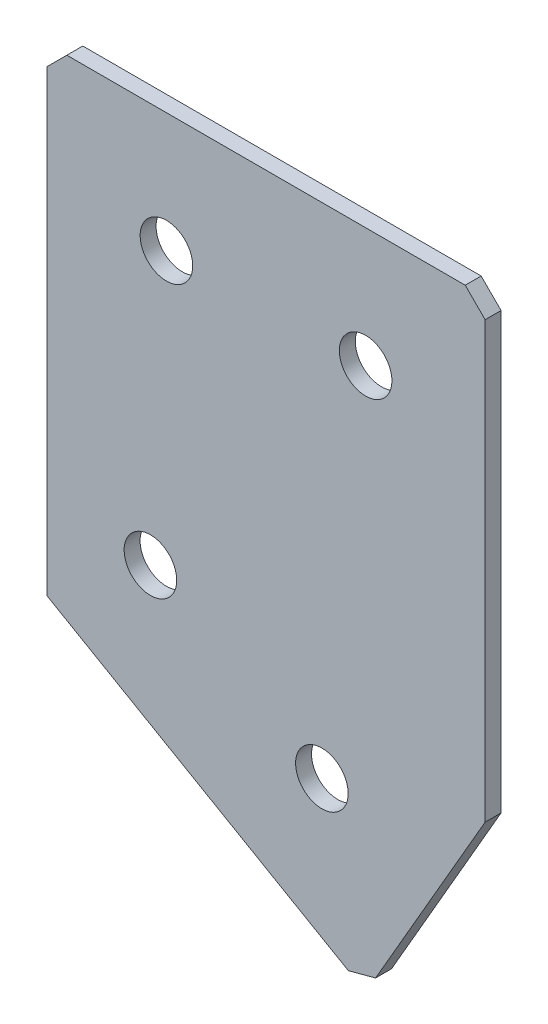
SolidWorks part; units mm, degrees
material "Простая углеродистая сталь"
ref_plane "Спереди" through (0, 0, 0) normal (0, 0, 1) x (1, 0, 0)
ref_plane "Сверху" through (0, 0, 0) normal (0, 1, 0) x (1, 0, 0)
ref_plane "Справа" through (0, 0, 0) normal (1, 0, 0) x (0, 0, -1)
sketch "Эскиз3" plane through (0, 0, 0) normal (0, 0, -1) x (1, 0, 0)
  line L0 (0, 0) -> (55, 0)
  line L1 (55, 0) -> (55, 57.1132)
  line L2 (0, 0) -> (0, 60)
  line L3 (0, 60) -> (40, 83.094)
  line L4 (40, 83.094) -> (55, 57.1132)
  dimension "D1" = 55
  dimension "D2" = 60
  dimension "D3" = 30
  dimension "D4" = 30
  dimension "D5" = 57.1132
extrude "Бобышка-Вытянуть1" add sketch "Эскиз3" along normal blind 2
hole_wizard "Отверстие с зазором M61" positions "Эскиз4" profile "Эскиз5" hole size "M6" standard "DIN" end condition through all
sketch "Эскиз4" plane through (0, 0, -2) normal (0, 0, -1) x (1, 0, 0)
  line L0 (12.9904, 50.1795) -> (34.5096, 62.6036) construction
  line L2 (40, 83.094) -> (0, 60) construction
  line L3 (15, 15) -> (40, 15) construction
  line L5 (0, 0) -> (55, 0) construction
  line L6 (0, 60) -> (0, 0) construction
  line L7 (55, 0) -> (55, 57.1132) construction
  line L8 (55, 57.1132) -> (40, 83.094) construction
  line L9 (12.9904, 50.1795) -> (0, 42.6795) construction
  point P0 (15, 15)
  point P2 (40, 15)
  point P4 (12.9904, 50.1795)
  point P6 (34.5096, 62.6036)
  dimension "D1" = 15
  dimension "D2" = 15
  dimension "D3" = 15
  dimension "D4" = 15
  dimension "D5" = 15
  dimension "D6" = 15
  dimension "D7" = 24.8483
  dimension "D8" = 25
sketch "Эскиз5" plane through (15, -15, -2) normal (1, 0, 0) x (0, 1, 0)
  line L0 (0, 0) -> (0, 2)
  line L1 (0, 2) -> (3.3, 2)
  line L2 (3.3, 2) -> (3.3, 0)
  line L5 (3.3, 0) -> (0, 0)
  line L11 (0, -6.35) -> (0, 107.95) construction
  dimension "Диаметр сквозного отверстия" = 6.6
  dimension "Глубина сквозного отверстия" = 2
chamfer "Фаска1" distance 2.5 distance2 2.5 3 edges at (40, -83.094, -1) (55, 0, -1) (0, 0, -1)
